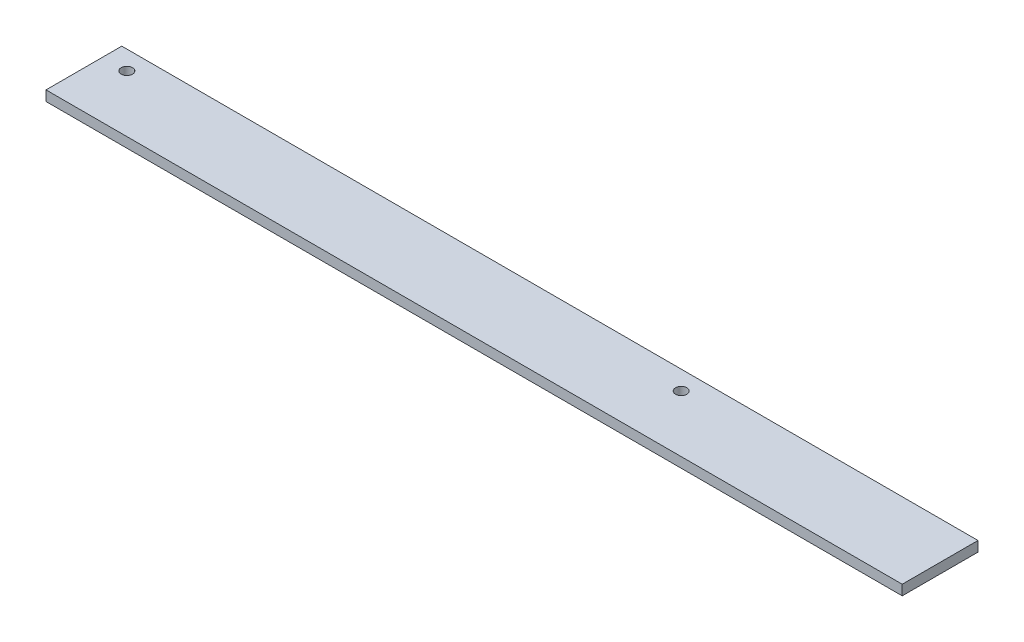
SolidWorks part; units mm, degrees
ref_plane "Спереди" through (0, 0, 0) normal (0, 0, 1) x (1, 0, 0)
ref_plane "Сверху" through (0, 0, 0) normal (0, 1, 0) x (1, 0, 0)
ref_plane "Справа" through (0, 0, 0) normal (1, 0, 0) x (0, 0, -1)
sketch "Эскиз1" plane through (0, 0, 0) normal (1, 0, 0) x (0, 0, -1)
  line L1 (-15, -2) -> (15, -2)
  line L2 (-15, -2) -> (-15, 2)
  line L3 (-15, 2) -> (15, 2)
  line L4 (15, -2) -> (15, 2)
  line L5 (-15, -2) -> (15, 2) construction
  line L6 (-15, 2) -> (15, -2) construction
  point P0 (0, 0)
  dimension "D1" = 4
  dimension "D2" = 30
extrude "Бобышка-Вытянуть1" add sketch "Эскиз1" along normal blind 339
sketch "Эскиз2" plane through (0, 2, 0) normal (0, 1, 0) x (1, 0, 0)
  line L0 (0, 15) -> (0, -15) construction
  line L1 (339, 15) -> (0, 15) construction
  line L2 (339, 15) -> (339, -15) construction
  circle A0 centre (9.5, 7.5) radius 2.25
  circle A1 centre (229, 7.5) radius 2.25
  dimension "D1" = 4.5
  dimension "D2" = 9.5
  dimension "D3" = 7.5
  dimension "D4" = 4.5
  dimension "D5" = 110
  dimension "D6" = 7.5
extrude "Вырез-Вытянуть1" cut sketch "Эскиз2" against normal through all
